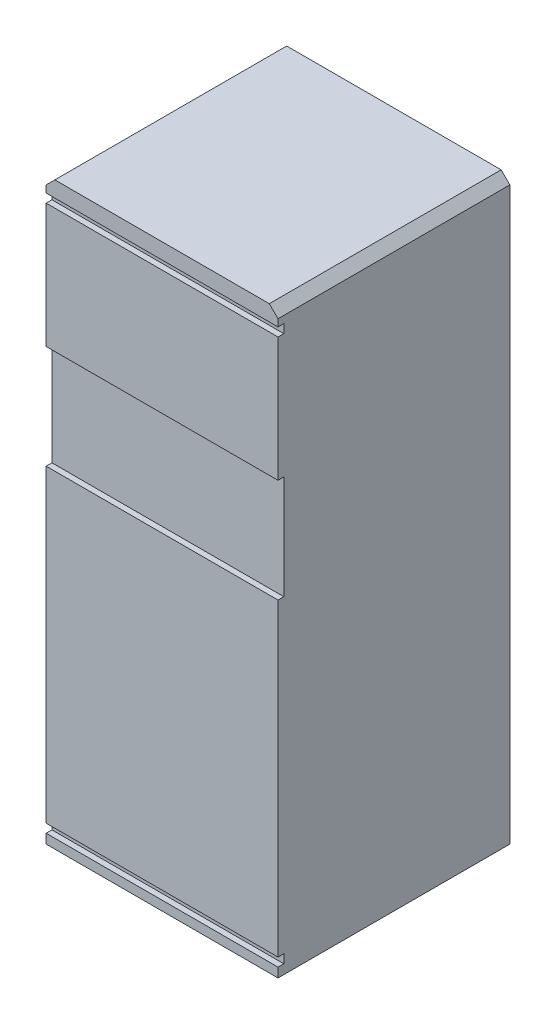
SolidWorks part; units mm, degrees
ref_plane "Alzado" through (0, 0, 0) normal (0, 0, 1) x (1, 0, 0)
ref_plane "Planta" through (0, 0, 0) normal (0, 1, 0) x (1, 0, 0)
ref_plane "Vista lateral" through (0, 0, 0) normal (1, 0, 0) x (0, 0, -1)
sketch "Croquis1" plane through (0, 0, 0) normal (0, 1, 0) x (1, 0, 0)
  line L1 (-400, 400) -> (400, 400)
  line L2 (-400, 400) -> (-400, -400)
  line L3 (-400, -400) -> (400, -400)
  line L4 (400, 400) -> (400, -400)
  line L5 (-400, 400) -> (400, -400) construction
  line L6 (-400, -400) -> (400, 400) construction
  point P0 (0, 0)
  dimension "D1" = 800
  dimension "D2" = 800
extrude "Saliente-Extruir1" add sketch "Croquis1" along normal blind 2000
sketch "Croquis2" plane through (0, 0, 400) normal (0, 0, 1) x (1, 0, 0)
  line L0 (-453.1055, 1895.5127) -> (-453.1055, 82.6025)
  line L1 (-403.1055, 1915.5127) -> (426.2386, 1915.5127)
  line L2 (-423.1055, 1895.5127) -> (-423.1055, 1487.1562)
  line L3 (-403.1055, 62.6025) -> (426.2386, 62.6025)
  line L4 (446.2386, 1895.5127) -> (446.2386, 1487.1562)
  line L5 (-423.1055, 1915.5127) -> (446.2386, 62.6025) construction
  line L6 (-423.1055, 62.6025) -> (446.2386, 1915.5127) construction
  line L7 (-403.1055, 32.6025) -> (426.2386, 32.6025)
  line L8 (476.2386, 1895.5127) -> (476.2386, 82.6025)
  line L9 (-403.1055, 1945.5127) -> (426.2386, 1945.5127)
  line L10 (-423.1055, 1129.4484) -> (446.2386, 1129.4484)
  line L12 (446.2386, 1487.1562) -> (-423.1055, 1487.1562)
  line L13 (-423.1055, 1129.4484) -> (-423.1055, 82.6025)
  line L14 (-423.1055, 1895.5127) -> (-423.1055, 82.6025) construction
  line L15 (446.2386, 1129.4484) -> (446.2386, 82.6025)
  line L16 (446.2386, 1895.5127) -> (446.2386, 82.6025) construction
  arc A0 (-423.1055, 82.6025) -> (-403.1055, 62.6025) centre (-403.1055, 82.6025) ccw
  arc A1 (426.2386, 62.6025) -> (446.2386, 82.6025) centre (426.2386, 82.6025) ccw
  arc A2 (-403.1055, 1915.5127) -> (-423.1055, 1895.5127) centre (-403.1055, 1895.5127) ccw
  arc A3 (426.2386, 1915.5127) -> (446.2386, 1895.5127) centre (426.2386, 1895.5127) cw
  arc A4 (-453.1055, 82.6025) -> (-403.1055, 32.6025) centre (-403.1055, 82.6025) ccw
  arc A5 (426.2386, 32.6025) -> (476.2386, 82.6025) centre (426.2386, 82.6025) ccw
  arc A6 (426.2386, 1945.5127) -> (476.2386, 1895.5127) centre (426.2386, 1895.5127) cw
  arc A7 (-403.1055, 1945.5127) -> (-453.1055, 1895.5127) centre (-403.1055, 1895.5127) ccw
  point P0 (11.5665, 989.0576)
  dimension "D1" = 20
  dimension "D2" = 30
extrude "Cortar-Extruir1" cut sketch "Croquis2" against normal blind 20
chamfer "Chaflán1" distance 30 angle 45 2 edges at (-400, 2000, 0) (400, 2000, 0)
